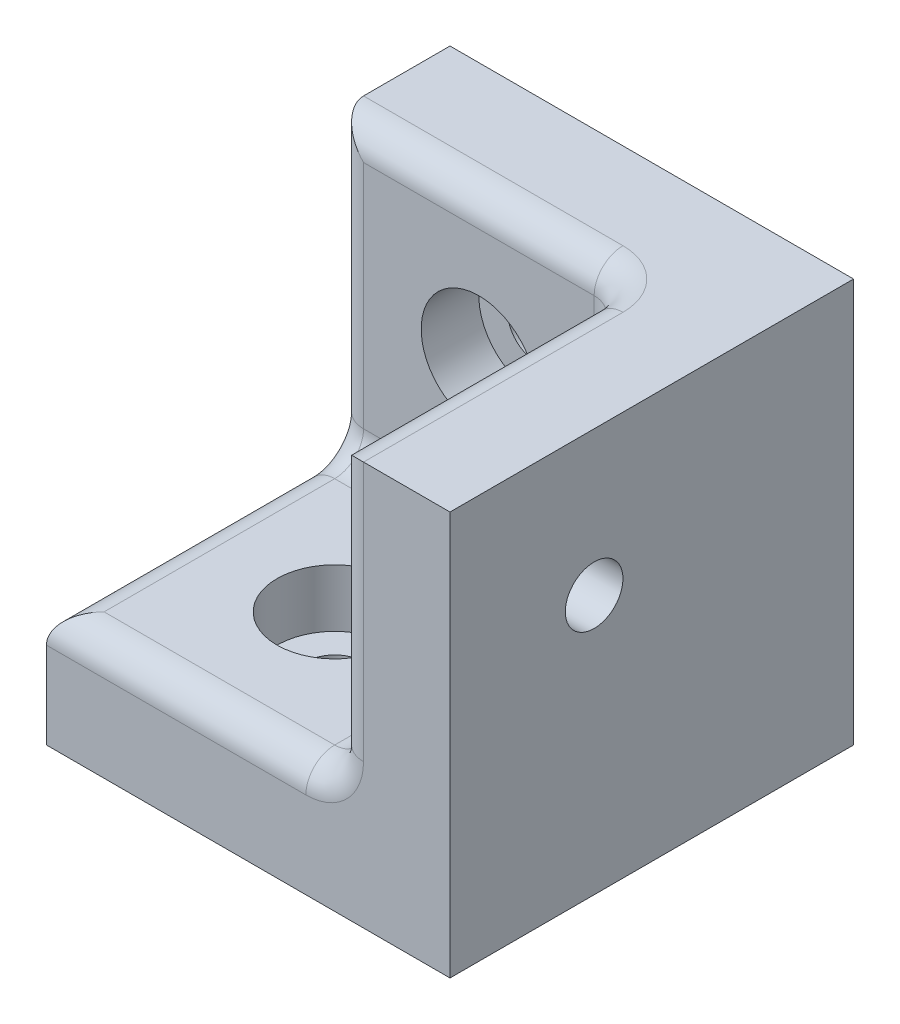
SolidWorks part; units mm, degrees
ref_plane "Plan de face" through (0, 0, 0) normal (0, 0, 1) x (1, 0, 0)
ref_plane "Plan de dessus" through (0, 0, 0) normal (0, 1, 0) x (1, 0, 0)
ref_plane "Plan de droite" through (0, 0, 0) normal (1, 0, 0) x (0, 0, -1)
sketch "Esquisse1" plane through (0, 0, 0) normal (0, 0, 1) x (1, 0, 0)
  line L1 (-5, 14) -> (5, 14)
  line L2 (-5, 14) -> (-5, 0)
  line L3 (-5, 0) -> (5, 0)
  line L4 (5, 14) -> (5, 0)
  dimension "D1" = 10
  dimension "D2" = 14
  dimension "D3" = 5
extrude "Boss.-Extru.1" add sketch "Esquisse1" along normal blind 4
sketch "Esquisse2" plane through (0, 0, 4) normal (0, 0, 1) x (1, 0, 0)
  line L0 (5, 0) -> (5, 14) construction
  line L1 (-5, 0) -> (5, 0)
  line L2 (-5, 0) -> (-5, 4)
  line L3 (-5, 4) -> (5, 4)
  line L4 (5, 0) -> (5, 4)
  dimension "D1" = 4
extrude "Boss.-Extru.2" add sketch "Esquisse2" along normal blind 10
sketch "Esquisse3" plane through (0, 0, 4) normal (0, 0, 1) x (1, 0, 0)
  line L0 (5, 14) -> (-5, 14) construction
  line L1 (-5, 14) -> (-5, 4) construction
  circle A0 centre (0, 9) radius 1
  point P2 (0, 14)
  point P3 (-5, 9)
  dimension "D1" = 2
extrude "Enlèv. mat.-Extru.1" cut sketch "Esquisse3" against normal through all
sketch "Esquisse4" plane through (0, 4, 0) normal (0, 1, 0) x (1, 0, 0)
  line L0 (5, -14) -> (-5, -14) construction
  line L1 (-5, -14) -> (-5, -4) construction
  circle A0 centre (0, -9) radius 1
  point P0 (0, -14)
  point P1 (-5, -9)
  dimension "D1" = 2
extrude "Enlèv. mat.-Extru.2" cut sketch "Esquisse4" against normal through all
sketch "Esquisse5" plane through (0, 0, 4) normal (0, 0, 1) x (1, 0, 0)
  circle A0 centre (0, 9) radius 2
  dimension "D1" = 4
extrude "Enlèv. mat.-Extru.3" cut sketch "Esquisse5" against normal blind 2
sketch "Esquisse6" plane through (0, 4, 0) normal (0, 1, 0) x (1, 0, 0)
  circle A0 centre (0, -9) radius 2
  dimension "D1" = 4
extrude "Enlèv. mat.-Extru.4" cut sketch "Esquisse6" against normal blind 2
sketch "Esquisse7" plane through (5, 0, 0) normal (1, 0, 0) x (0, 0, -1)
  line L0 (-14, 0) -> (-14, 14)
  line L1 (0, 14) -> (-14, 14)
  line L6 (0, 0) -> (0, 14)
  line L7 (0, 14) -> (-4, 14)
  line L8 (-4, 14) -> (-4, 4)
  line L9 (-4, 4) -> (-14, 4)
  line L10 (-14, 4) -> (-14, 0)
  line L11 (-14, 0) -> (0, 0)
  line L12 (0, 0) -> (0, 14)
  line L17 (-14, 0) -> (0, 0)
  dimension "D1" = 0
extrude "Boss.-Extru.3" add sketch "Esquisse7" along normal blind 4
sketch "Esquisse8" plane through (5, 0, 0) normal (-1, 0, 0) x (0, 0, 1)
  line L0 (4, 4) -> (4, 14) construction
  line L1 (14, 4) -> (4, 4) construction
  circle A0 centre (9, 9) radius 1
  point P2 (4, 9)
  point P3 (9, 4)
  point P6 (0, 0)
  point P9 (0, 0)
  point P10 (0, 0)
  dimension "D1" = 2
extrude "Enlèv. mat.-Extru.5" cut sketch "Esquisse8" against normal through all
sketch "Esquisse9" plane through (5, 0, 0) normal (-1, 0, 0) x (0, 0, 1)
  circle A0 centre (9, 9) radius 2
  dimension "D1" = 4
extrude "Enlèv. mat.-Extru.6" cut sketch "Esquisse9" against normal blind 2
fillet "Congé1" radius 1 9 edges at (0, 4, 4) (-5, 9, 4) (0, 4, 14) (-5, 4, 9) (0, 14, 4) (5, 14, 9) (5, 9, 14) (5, 9, 4) (5, 4, 9)
